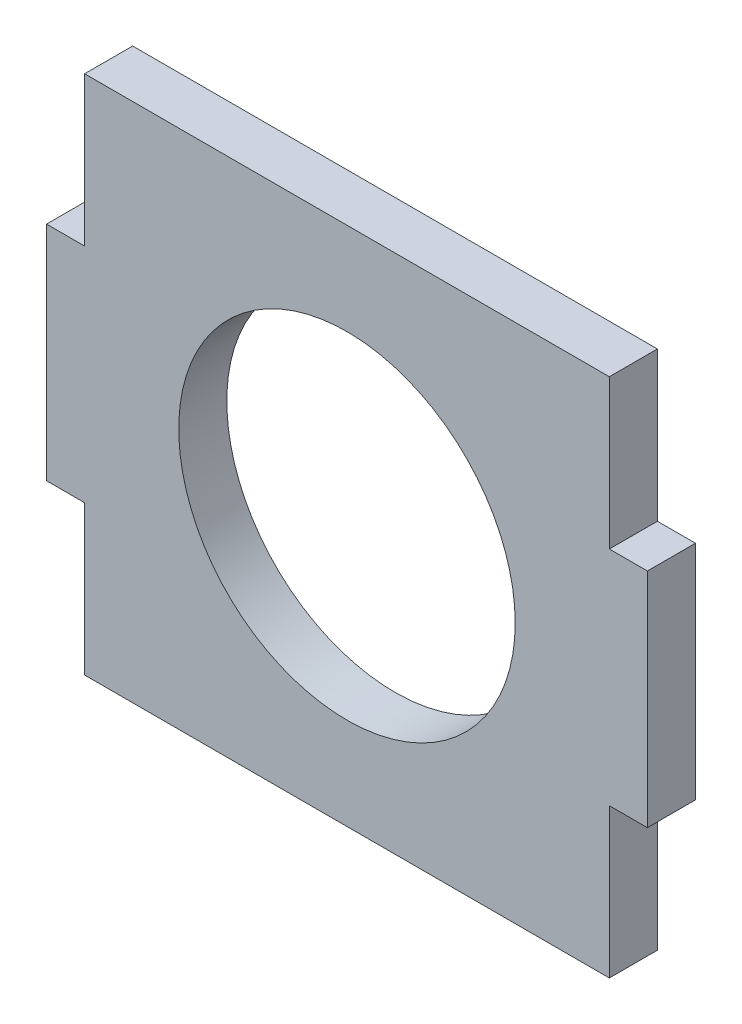
SolidWorks part; units mm, degrees
ref_plane "Alzado" through (0, 0, 0) normal (0, 0, 1) x (1, 0, 0)
ref_plane "Planta" through (0, 0, 0) normal (0, 1, 0) x (1, 0, 0)
ref_plane "Vista lateral" through (0, 0, 0) normal (1, 0, 0) x (0, 0, -1)
sketch "Croquis1" plane through (0, 0, 0) normal (0, 0, 1) x (1, 0, 0)
  line L0 (-7.5, 6.5) -> (7.5, -6.5) construction
  line L1 (-7.5, 6.5) -> (7.5, 6.5)
  line L2 (-7.5, 6.5) -> (-7.5, -6.5)
  line L3 (-7.5, -6.5) -> (7.5, -6.5)
  line L4 (7.5, 6.5) -> (7.5, -6.5)
  point P4 (0, 0)
  dimension "D1" = 15
  dimension "D2" = 13
extrude "Saliente-Extruir1" add sketch "Croquis1" along normal blind 1.2
sketch "Croquis2" plane through (0, 0, 1.2) normal (0, 0, 1) x (1, 0, 0)
  line L0 (-7.5, 6.5) -> (-7.5, -6.5) construction
  line L1 (7.5, 6.5) -> (6.55, 6.5)
  line L2 (7.5, 6.5) -> (7.5, 2.775)
  line L3 (7.5, 2.775) -> (6.55, 2.775)
  line L4 (6.55, 6.5) -> (6.55, 2.775)
  line L5 (7.5, -6.5) -> (6.55, -6.5)
  line L6 (7.5, -6.5) -> (7.5, -2.775)
  line L7 (7.5, -2.775) -> (6.55, -2.775)
  line L8 (6.55, -6.5) -> (6.55, -2.775)
  line L9 (-7.5, -6.5) -> (-6.55, -6.5)
  line L10 (-7.5, -6.5) -> (-7.5, -2.775)
  line L11 (-7.5, -2.775) -> (-6.55, -2.775)
  line L12 (-6.55, -6.5) -> (-6.55, -2.775)
  line L13 (-7.5, 6.5) -> (-6.55, 6.5)
  line L14 (-7.5, 6.5) -> (-7.5, 2.775)
  line L15 (-7.5, 2.775) -> (-6.55, 2.775)
  line L16 (-6.55, 6.5) -> (-6.55, 2.775)
  dimension "D1" = 13.1
  dimension "D2" = 5.55
extrude "Cortar-Extruir1" cut sketch "Croquis2" against normal up to next
sketch "Croquis3" plane through (0, 0, 1.2) normal (0, 0, 1) x (1, 0, 0)
  circle A0 centre (0, 0) radius 4.2
  dimension "D1" = 8.4
extrude "Cortar-Extruir2" cut sketch "Croquis3" against normal up to next
